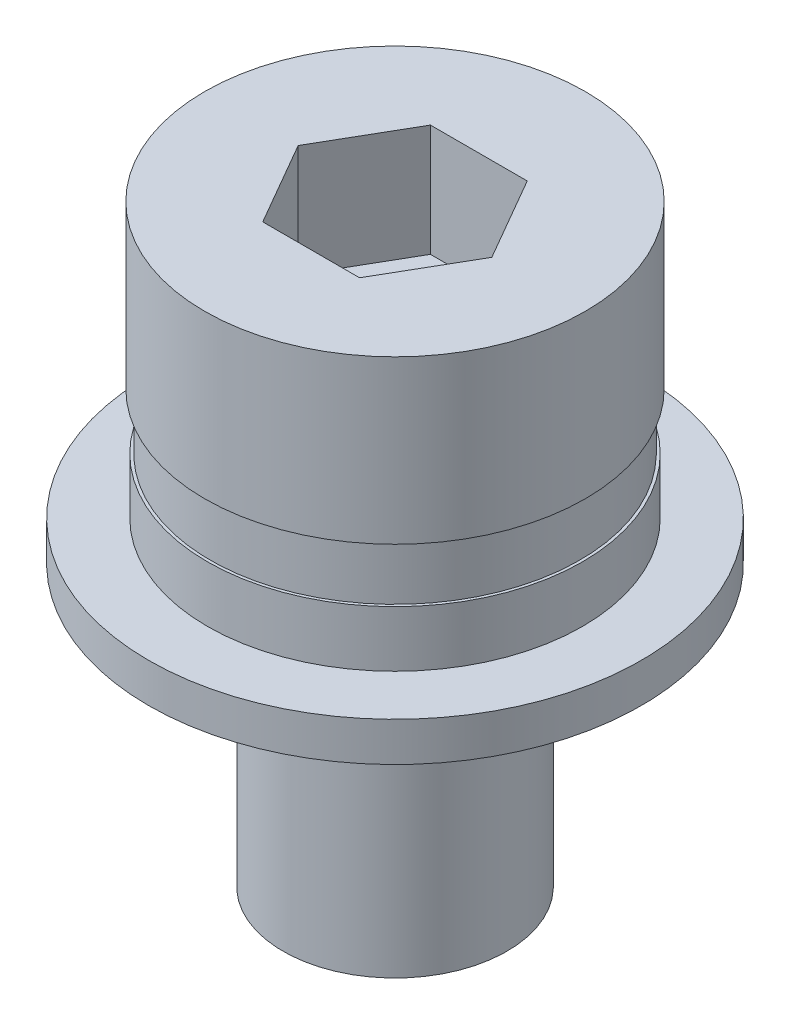
SolidWorks part; units mm, degrees
other "标注1"
sketch "草图7" plane through (4.4, 5.6, 4.4) normal (0.6477, 0.4057, 0.6449) x (0.605, 0.2405, -0.759)
other "细节项目1"
ref_plane "前视基准面" through (0, 0, 0) normal (0, 0, 1) x (1, 0, 0)
ref_plane "上视基准面" through (0, 0, 0) normal (0, 1, 0) x (1, 0, 0)
ref_plane "右视基准面" through (0, 0, 0) normal (1, 0, 0) x (0, 0, -1)
sketch "草图1" plane through (0, 0, 0) normal (0, 1, 0) x (1, 0, 0)
  circle A0 centre (0, 0) radius 4.4
  dimension "D1" = 8.8
extrude "凸台-拉伸1" add sketch "草图1" along normal blind 0.7
sketch "草图2" plane through (0, 0.7, 0) normal (0, 1, 0) x (1, 0, 0)
  circle A0 centre (0, 0) radius 3.35
  dimension "D1" = 6.7
extrude "凸台-拉伸2" add sketch "草图2" along normal blind 1
sketch "草图3" plane through (0, 1.7, 0) normal (0, 1, 0) x (1, 0, 0)
  circle A0 centre (0, 0) radius 3.4
  dimension "D1" = 6.8
extrude "凸台-拉伸3" add sketch "草图3" along normal blind 3.9
sketch "草图4" plane through (0, 1.7, 0) normal (0, -1, 0) x (1, 0, 0)
  circle A0 centre (0, 0) radius 3.3
  circle A1 centre (0, 0) radius 10.5263
  dimension "D1" = 6.6
extrude "切除-拉伸1" cut sketch "草图4" against normal blind 1
sketch "草图5" plane through (0, 5.6, 0) normal (0, 1, 0) x (1, 0, 0)
  line L1 (-1.7293, 0) -> (-0.8647, -1.4976)
  line L2 (-0.8647, -1.4976) -> (0.8647, -1.4976)
  line L3 (0.8647, -1.4976) -> (1.7293, 0)
  line L4 (1.7293, 0) -> (0.8647, 1.4976)
  line L5 (0.8647, 1.4976) -> (-0.8647, 1.4976)
  line L6 (-0.8647, 1.4976) -> (-1.7293, 0)
  circle A0 centre (0, 0) radius 1.4976 construction
extrude "切除-拉伸2" cut sketch "草图5" against normal blind 2
sketch "草图6" plane through (0, 0, 0) normal (0, -1, 0) x (1, 0, 0)
  circle A0 centre (0, 0) radius 2
  dimension "D1" = 4
extrude "凸台-拉伸4" add sketch "草图6" along normal blind 5
